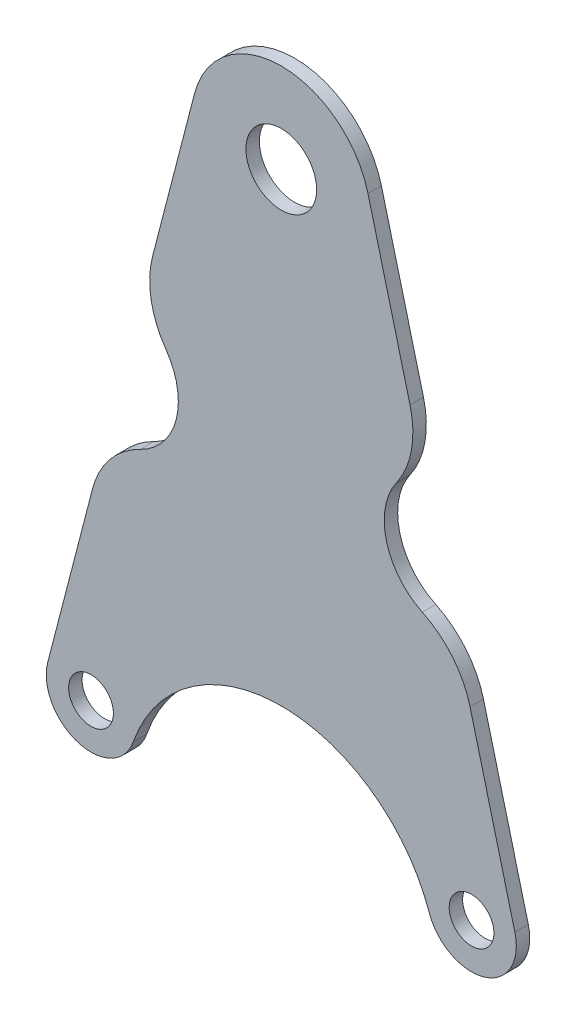
SolidWorks part; units mm, degrees
ref_plane "Спереди" through (0, 0, 0) normal (0, 0, 1) x (1, 0, 0)
ref_plane "Сверху" through (0, 0, 0) normal (0, 1, 0) x (1, 0, 0)
ref_plane "Справа" through (0, 0, 0) normal (1, 0, 0) x (0, 0, -1)
sketch "Эскиз1" plane through (0, 0, 0) normal (0, 0, 1) x (1, 0, 0)
  line L0 (0, 20) -> (0, -181.3933) construction
  line L6 (-19.3591, 5.0223) -> (-52.1796, -121.4889)
  line L8 (19.3591, 5.0223) -> (52.1796, -121.4889)
  circle A0 centre (0, 0) radius 7.9
  circle A1 centre (-42.5, -124) radius 5
  arc A2 (-19.3591, 5.0223) -> (19.3591, 5.0223) centre (0, 0) cw
  arc A3 (-52.1796, -121.4889) -> (-33.0556, -127.2867) centre (-42.5, -124) ccw
  circle A5 centre (42.5, -124) radius 5
  arc A6 (52.1796, -121.4889) -> (33.0556, -127.2867) centre (42.5, -124) cw
  arc A8 (-33.0556, -127.2867) -> (33.0556, -127.2867) centre (0, -138.7902) cw
  point P8 (0, -134)
  point P19 (0, -134)
  dimension "D1" = 15.8
  dimension "D4" = 20
  dimension "D6" = 10
  dimension "D5" = 10
  dimension "D7" = 35
  dimension "D2" = 85
  dimension "D3" = 124
extrude "Бобышка-Вытянуть1" add sketch "Эскиз1" along normal blind 3
sketch "Эскиз2" plane through (0, 0, 3) normal (0, 0, 1) x (1, 0, 0)
  line L0 (0, -16) -> (0, -54) construction
  line L1 (8.05, -16) -> (8.05, -54) construction
  line L2 (-8.05, -16) -> (-8.05, -54) construction
  line L3 (4, -34.05) -> (-4, -34.05)
  line L4 (0, 0) -> (0, -65.5898) construction
  arc A3 (8.05, -16) -> (-8.05, -16) centre (0, -16) ccw construction
  arc A8 (8.05, -16) -> (9.8293, -20.4483) centre (14.5, -16) ccw
  arc A9 (-8.05, -54) -> (8.05, -54) centre (0, -54) ccw construction
  arc A10 (9.8293, -20.4483) -> (4, -34.05) centre (4, -26) cw
  arc A11 (8.05, -16) -> (-8.05, -16) centre (0, -16) ccw
  arc A12 (-9.8293, -20.4483) -> (-4, -34.05) centre (-4, -26) ccw
  arc A13 (-8.05, -16) -> (-9.8293, -20.4483) centre (-14.5, -16) cw
  point P8 (0, -35)
  point P20 (0, -34.05)
  dimension "D1" = 16
  dimension "D2" = 8.05
  dimension "D4" = 16.1
  dimension "D7" = 38
  dimension "D3" = 8
  dimension "D5" = 26
extrude "Вырез-Вытянуть1" [suppressed] cut sketch "Эскиз2" against normal blind 4.5
sketch "Эскиз3" plane through (0, 0, 3) normal (0, 0, 1) x (1, 0, 0)
  line L0 (0, 0) -> (0, -88.8714) construction
  circle A0 centre (-38, -56.3915) radius 15
  circle A1 centre (38, -56.3915) radius 15
  circle A2 centre (0, -37.4415) radius 5 construction
  dimension "D1" = 68
  dimension "D2" = 30
  dimension "D4" = 10
  dimension "D3" = 38
extrude "Вырез-Вытянуть2" cut sketch "Эскиз3" against normal through all
fillet "Скругление1" radius 20 4 edges at (31.7536, -42.7539, 1.5) (39.1711, -71.3457, 1.5) (-39.1711, -71.3457, 1.5) (-31.7536, -42.7539, 1.5)
